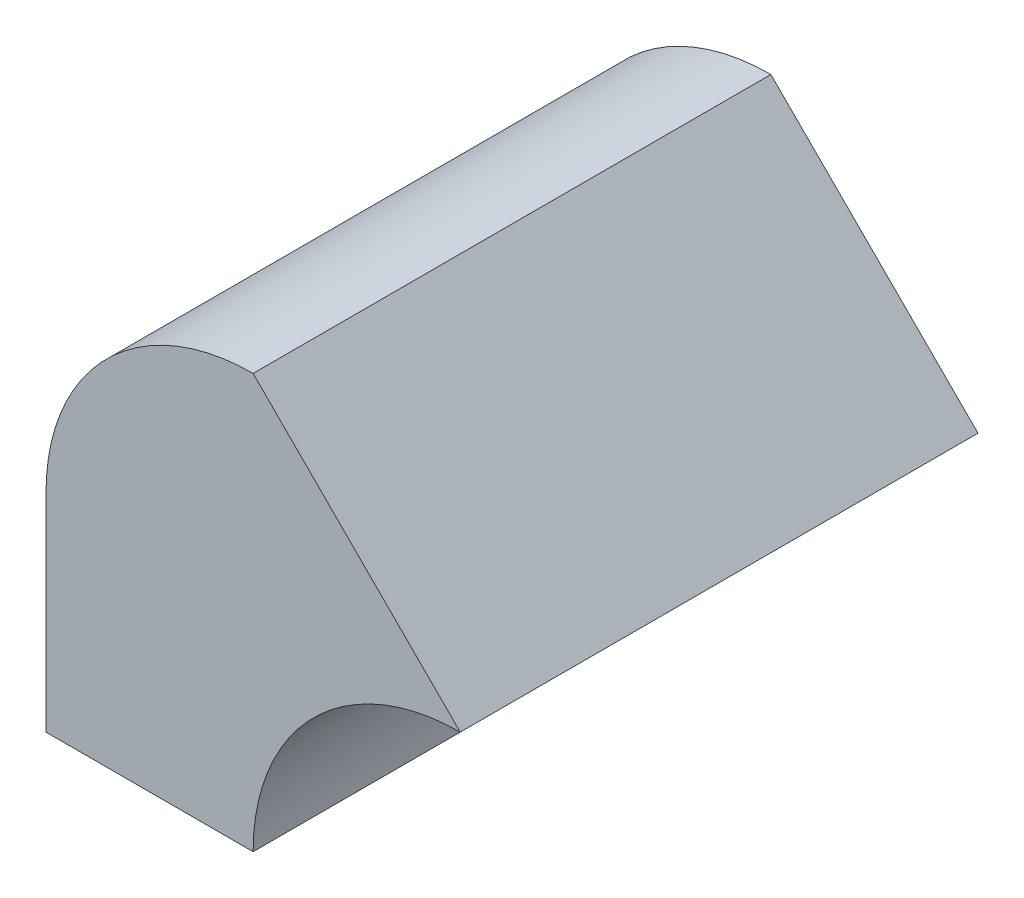
SolidWorks part; units mm, degrees
ref_plane "Front Plane" through (0, 0, 0) normal (0, 0, 1) x (1, 0, 0)
ref_plane "Top Plane" through (0, 0, 0) normal (0, 1, 0) x (1, 0, 0)
ref_plane "Right Plane" through (0, 0, 0) normal (1, 0, 0) x (0, 0, -1)
sketch "Sketch1" plane through (0, 0, 0) normal (0, 0, 1) x (1, 0, 0)
  line L0 (0, -10) -> (0, 0)
  line L1 (0, -10) -> (10, -10)
  line L2 (20, 0) -> (10, 10)
  arc A0 (10, -10) -> (20, 0) centre (20, -10) cw
  arc A1 (0, 0) -> (10, 10) centre (10, 0) cw
  dimension "D5" = 10
  dimension "D1" = 10
  dimension "D2" = 10
  dimension "D3" = 10
  dimension "D4" = 10
extrude "Boss-Extrude1" add sketch "Sketch1" along normal blind 25
